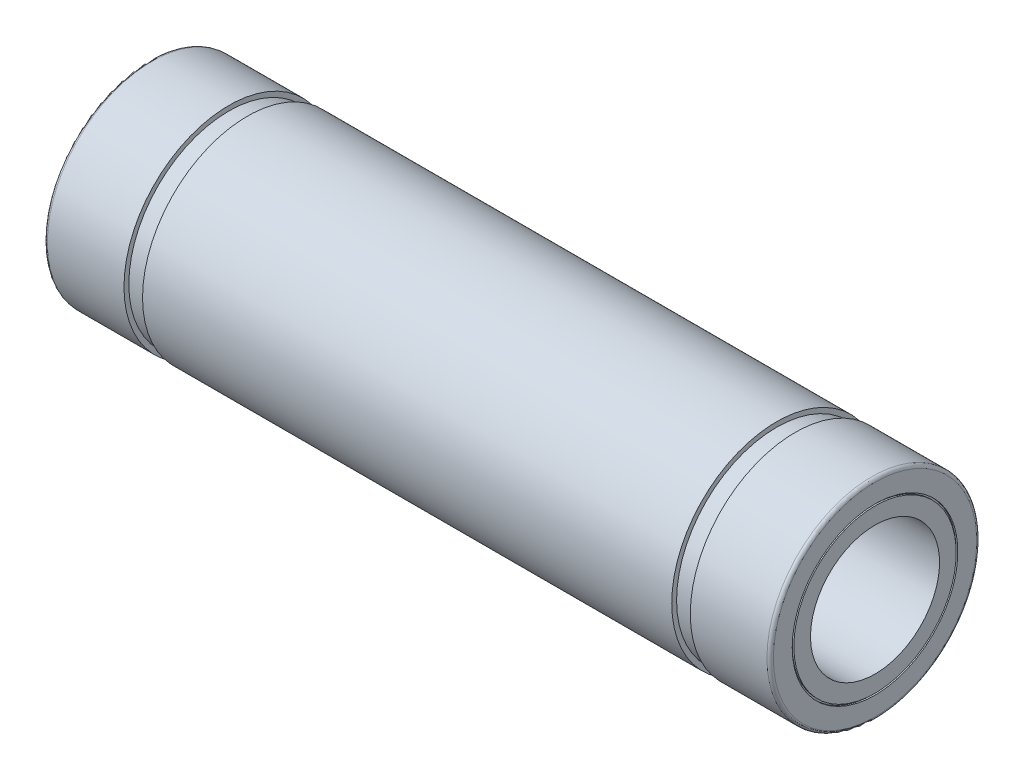
SolidWorks part; units mm, degrees
ref_plane "Front Plane" through (0, 0, 0) normal (0, 0, 1) x (1, 0, 0)
ref_plane "Top Plane" through (0, 0, 0) normal (0, 1, 0) x (1, 0, 0)
ref_plane "Right Plane" through (0, 0, 0) normal (1, 0, 0) x (0, 0, -1)
ref_plane "Plane1" through (0, 0, 0) normal (0, 0, -1) x (-1, 0, 0)
sketch "Sketch1" plane through (0, 0, 0) normal (0, 0, -1) x (-1, 0, 0)
  line L0 (-22.4, 5.0333) -> (-22.5, 5.0333)
  line L1 (-22.5, 5.0333) -> (-22.5, 4)
  line L2 (-22.5, 4) -> (22.5, 4)
  line L3 (22.5, 4) -> (22.5, 5.0333)
  line L4 (22.5, 5.0333) -> (22.4, 5.0333)
  line L5 (22.4, 5.0333) -> (22.4, 5.1333)
  line L6 (22.4, 5.1333) -> (22.5, 5.1333)
  line L7 (22.5, 5.1333) -> (22.5, 6.3)
  line L8 (22.3, 6.5) -> (17.55, 6.5)
  line L9 (17.55, 6.5) -> (17.55, 6.2)
  line L10 (17.55, 6.2) -> (16.4, 6.2)
  line L11 (16.4, 6.2) -> (16.4, 6.5)
  line L12 (16.4, 6.5) -> (-16.4, 6.5)
  line L13 (-16.4, 6.5) -> (-16.4, 6.2)
  line L14 (-16.4, 6.2) -> (-17.55, 6.2)
  line L15 (-17.55, 6.2) -> (-17.55, 6.5)
  line L16 (-17.55, 6.5) -> (-22.3, 6.5)
  line L17 (-22.5, 6.3) -> (-22.5, 5.1333)
  line L18 (-22.5, 5.1333) -> (-22.4, 5.1333)
  line L19 (-22.4, 5.1333) -> (-22.4, 5.0333)
  line L20 (-22.5, 0) -> (22.5, 0) construction
  arc A0 (22.5, 6.3) -> (22.3, 6.5) centre (22.3, 6.3) ccw
  arc A1 (-22.3, 6.5) -> (-22.5, 6.3) centre (-22.3, 6.3) ccw
revolve "Revolve1" add sketch "Sketch1" angle 360 about L20
